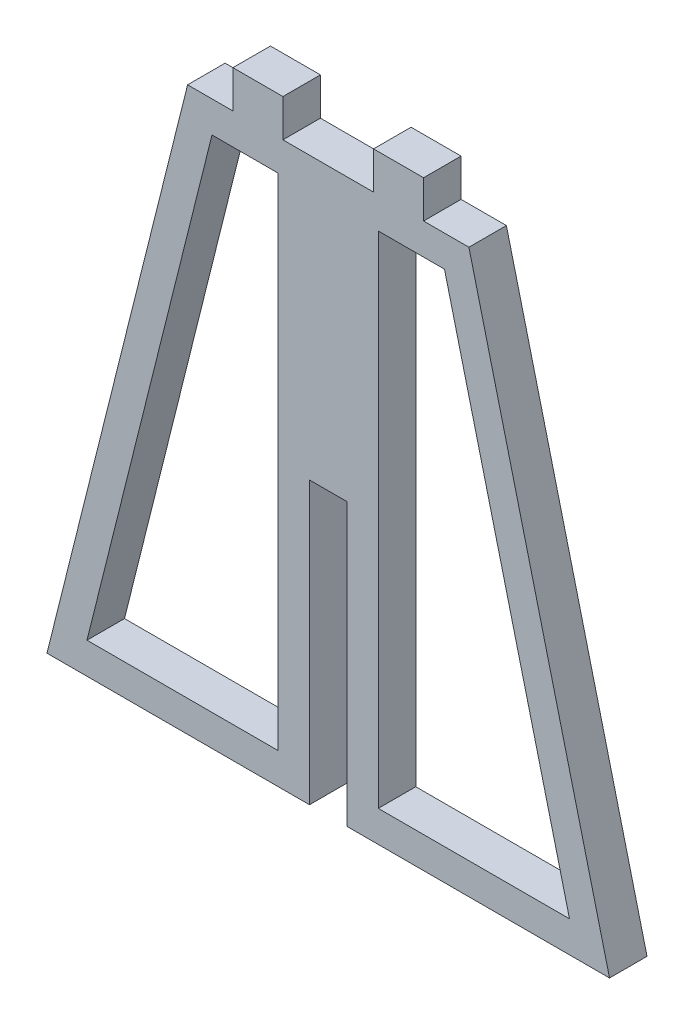
SolidWorks part; units mm, degrees
ref_plane "Front Plane" through (0, 0, 0) normal (0, 0, 1) x (1, 0, 0)
ref_plane "Top Plane" through (0, 0, 0) normal (0, 1, 0) x (1, 0, 0)
ref_plane "Right Plane" through (0, 0, 0) normal (1, 0, 0) x (0, 0, -1)
sketch "Sketch2" plane through (0, 0, 0) normal (0, 0, 1) x (1, 0, 0)
  line L0 (104.8846, 0) -> (0, 0) construction
  line L1 (-108.6923, 0) -> (0, 0) construction
  line L2 (0, 0) -> (0, 106.4423) construction
  line L3 (0, 0) -> (0, -93.6346) construction
  line L4 (45, 9.8654) -> (3, 9.8654)
  line L5 (-45, 9.8654) -> (-22.5, 99.8654)
  line L6 (-22.5, 99.8654) -> (-15.25, 99.8654)
  line L7 (22.5, 99.8654) -> (45, 9.8654)
  line L8 (11.25, 104.4253) -> (11.25, 94.3369) construction
  line L9 (-11.25, 104.4253) -> (-11.25, 94.8654) construction
  line L10 (-7.25, 105.8654) -> (-15.25, 105.8654)
  line L12 (7.25, 99.8654) -> (7.25, 105.8654)
  line L13 (7.25, 105.8654) -> (15.25, 105.8654)
  line L14 (15.25, 99.8654) -> (15.25, 105.8654)
  line L15 (6.2186, 54.8654) -> (-8.2199, 54.8654) construction
  line L16 (6.2186, 32.3654) -> (-8.2199, 32.3654) construction
  line L21 (-15.25, 99.8654) -> (-15.25, 105.8654)
  line L23 (-7.25, 99.8654) -> (-7.25, 105.8654)
  line L24 (-7.25, 99.8654) -> (7.25, 99.8654)
  line L25 (15.25, 99.8654) -> (22.5, 99.8654)
  line L26 (-3, 9.8654) -> (-45, 9.8654)
  line L27 (3, 54.8654) -> (-3, 54.8654)
  line L28 (3, 54.8654) -> (3, 9.8654)
  line L30 (-3, 54.8654) -> (-3, 9.8654)
  line L31 (-8, 94.8654) -> (-18.5961, 94.8654)
  line L32 (-18.5961, 94.8654) -> (-38.5961, 14.8654)
  line L33 (-38.5961, 14.8654) -> (-8, 14.8654)
  line L34 (-8, 14.8654) -> (-8, 94.8654)
  line L35 (38.5961, 14.8654) -> (8, 14.8654)
  line L36 (18.5961, 94.8654) -> (38.5961, 14.8654)
  line L37 (8, 94.8654) -> (18.5961, 94.8654)
  line L38 (8, 14.8654) -> (8, 94.8654)
  point P14 (11.25, 99.8654)
  point P19 (-11.25, 99.8654)
  point P28 (0, 32.3654)
  dimension "D1" = 90
  dimension "D2" = 90
  dimension "D3" = 45
  dimension "D4" = 45
  dimension "D5" = 11.25
  dimension "D6" = 11.25
  dimension "D7" = 4
  dimension "D8" = 4
  dimension "D9" = 11.25
  dimension "D10" = 22.5
  dimension "D11" = 45
  dimension "D12" = 22.5
  dimension "D13" = 6
  dimension "D14" = 6
  dimension "D15" = 8
  dimension "D16" = 5
  dimension "D17" = 5
  dimension "D18" = 5
extrude "Boss-Extrude4" add sketch "Sketch2" along normal blind 6
